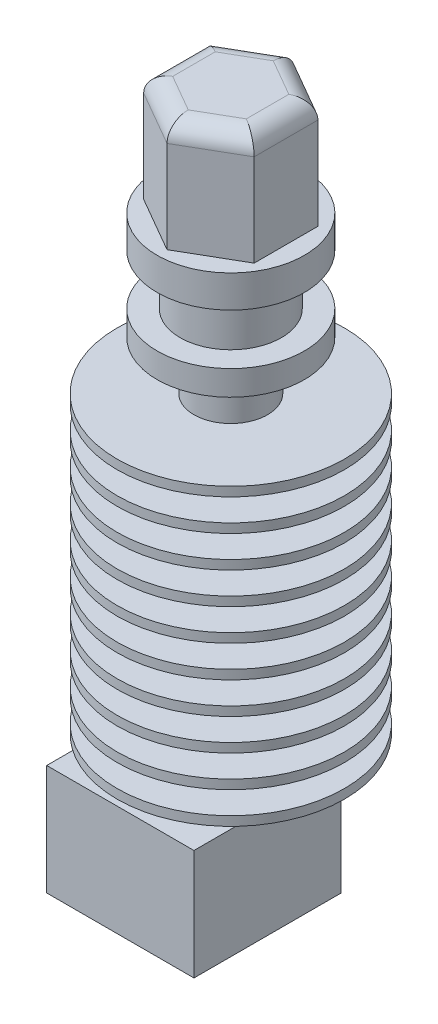
SolidWorks part; units mm, degrees
material "Liga 1060"
ref_plane "Plano frontal" through (0, 0, 0) normal (0, 0, 1) x (1, 0, 0)
ref_plane "Plano superior" through (0, 0, 0) normal (0, 1, 0) x (1, 0, 0)
ref_plane "Plano direito" through (0, 0, 0) normal (1, 0, 0) x (0, 0, -1)
sketch "Esboço1" plane through (0, 0, 0) normal (0, 0, 1) x (1, 0, 0)
  line L0 (0, 51.6592) -> (0, 1.6592)
  line L1 (0, 51.6592) -> (8, 51.6592)
  line L2 (8, 51.6592) -> (8, 48.1592)
  line L3 (5.5, 48.1592) -> (5.5, 42.6592)
  line L4 (5.5, 42.6592) -> (8, 42.6592)
  line L5 (8, 42.6592) -> (8, 39.9592)
  line L6 (8, 39.9592) -> (4, 39.9592)
  line L7 (5.5, 48.1592) -> (8, 48.1592)
  line L8 (4, 39.9592) -> (4, 34.6592)
  line L9 (4, 34.6592) -> (12.35, 34.6592)
  line L10 (12.35, 34.6592) -> (12.35, 33.6592)
  line L11 (12.35, 2.6592) -> (2, 2.6592)
  line L12 (2, 2.6592) -> (0, 2.6592) construction
  line L13 (2, 2.6592) -> (2, 1.6592)
  line L14 (2, 1.6592) -> (0, 1.6592)
  line L15 (0, 51.6592) -> (0, 1.6592) construction
  line L16 (12.35, 33.6592) -> (4, 33.6592)
  line L17 (4, 33.6592) -> (4, 31.2148)
  line L18 (4, 31.2148) -> (12.35, 31.2148)
  line L19 (12.35, 31.2148) -> (12.35, 30.2148)
  line L20 (12.35, 30.2148) -> (4, 30.2148)
  line L21 (4, 30.2148) -> (4, 27.7703)
  line L22 (4, 27.7703) -> (12.35, 27.7703)
  line L23 (12.35, 27.7703) -> (12.35, 26.7703)
  line L24 (12.35, 26.7703) -> (4, 26.7703)
  line L25 (4, 26.7703) -> (4, 24.3259)
  line L26 (4, 24.3259) -> (12.35, 24.3259)
  line L27 (12.35, 24.3259) -> (12.35, 23.3259)
  line L28 (12.35, 23.3259) -> (4, 23.3259)
  line L29 (4, 23.3259) -> (4, 20.8815)
  line L30 (4, 20.8815) -> (12.35, 20.8815)
  line L31 (12.35, 20.8815) -> (12.35, 19.8815)
  line L32 (12.35, 19.8815) -> (4, 19.8815)
  line L33 (4, 19.8815) -> (4, 17.437)
  line L34 (4, 17.437) -> (12.35, 17.437)
  line L35 (12.35, 17.437) -> (12.35, 16.437)
  line L36 (12.35, 16.437) -> (4, 16.437)
  line L37 (4, 16.437) -> (4, 13.9926)
  line L38 (4, 13.9926) -> (12.35, 13.9926)
  line L39 (12.35, 13.9926) -> (12.35, 12.9926)
  line L40 (12.35, 12.9926) -> (4, 12.9926)
  line L41 (4, 12.9926) -> (4, 10.5481)
  line L42 (4, 10.5481) -> (12.35, 10.5481)
  line L43 (12.35, 10.5481) -> (12.35, 9.5481)
  line L44 (12.35, 9.5481) -> (4, 9.5481)
  line L45 (4, 9.5481) -> (4, 7.1037)
  line L46 (4, 7.1037) -> (12.35, 7.1037)
  line L47 (12.35, 7.1037) -> (12.35, 6.1037)
  line L48 (12.35, 6.1037) -> (4, 6.1037)
  line L49 (4, 6.1037) -> (4, 3.6592)
  line L50 (4, 3.6592) -> (12.35, 3.6592)
  line L51 (12.35, 3.6592) -> (12.35, 2.6592)
  line L55 (4, 2.6592) -> (4, 0.2148) [skipped]
  line L56 (4, 0.2148) -> (12.35, 0.2148) [skipped]
  line L57 (12.35, 2.6592) -> (4, 2.6592) [skipped]
  dimension "D1" = 32
  dimension "D2" = 3.5
  dimension "D3" = 5.5
  dimension "D4" = 2.7
  dimension "D5" = 1
  dimension "D6" = 50
  dimension "D7" = 4
  dimension "D8" = 24.7
  dimension "D9" = 1
  dimension "D11" = 1
  dimension "D10" = 10
revolve "Revolução1" add sketch "Esboço1" angle 360 about L15
sketch "Esboço3" plane through (0, 1.6592, 0) normal (0, -1, 0) x (1, 0, 0)
  line L0 (0, 0) -> (0, 4) construction
  line L2 (-8, 12) -> (8, 12)
  line L3 (-8, 12) -> (-8, -4)
  line L4 (-8, -4) -> (8, -4)
  line L5 (8, 12) -> (8, -4)
  line L6 (-8, 12) -> (8, -4) construction
  line L7 (-8, -4) -> (8, 12) construction
extrude "Ressalto-extrusão1" add sketch "Esboço3" along normal blind 12
sketch "Esboço4" plane through (0, -10.3408, 0) normal (0, -1, 0) x (1, 0, 0)
  circle A0 centre (0, 0) radius 3
extrude "Ressalto-extrusão2" add sketch "Esboço4" along normal blind 5 draft 26
sketch "Esboço5" plane through (0, 51.6592, 0) normal (0, 1, 0) x (1, 0, 0)
  line L1 (0, -6.9282) -> (6, -3.4641)
  line L2 (6, -3.4641) -> (6, 3.4641)
  line L3 (6, 3.4641) -> (0, 6.9282)
  line L4 (0, 6.9282) -> (-6, 3.4641)
  line L5 (-6, 3.4641) -> (-6, -3.4641)
  line L6 (-6, -3.4641) -> (0, -6.9282)
  circle A0 centre (0, 0) radius 6 construction
  dimension "D1" = 12
extrude "Ressalto-extrusão3" add sketch "Esboço5" along normal blind 12
fillet "Filete1" radius 2 6 edges at (-6, 63.6592, 0) (-3, 63.6592, -5.1962) (3, 63.6592, -5.1962) (6, 63.6592, 0) (3, 63.6592, 5.1962) (-3, 63.6592, 5.1962)
